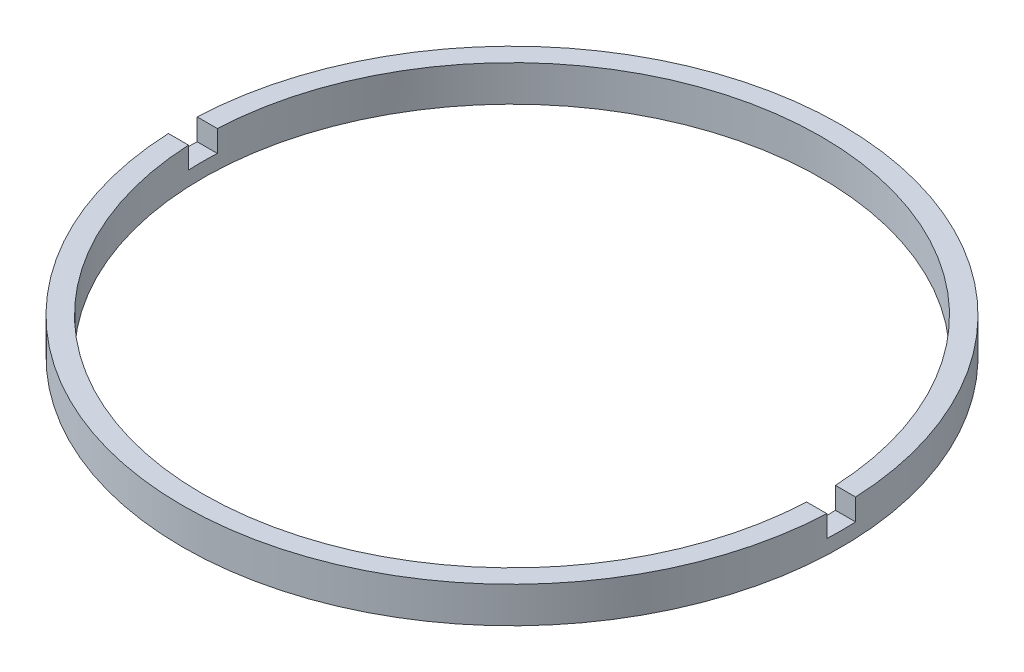
SolidWorks part; units mm, degrees
ref_plane "前视基准面" through (0, 0, 0) normal (0, 0, 1) x (1, 0, 0)
ref_plane "上视基准面" through (0, 0, 0) normal (0, 1, 0) x (1, 0, 0)
ref_plane "右视基准面" through (0, 0, 0) normal (1, 0, 0) x (0, 0, -1)
sketch "草图1" plane through (0, 0, 0) normal (0, 0, 1) x (1, 0, 0)
  line L0 (0, 56.2608) -> (0, -99.1922) construction
  line L1 (21.5, -1.9642) -> (22.9, -1.9642)
  line L4 (22.9, -1.9642) -> (22.9, -4.4642)
  line L5 (21.5, -4.4642) -> (21.5, -1.9642)
  line L7 (21.5, -4.4642) -> (22.9, -4.4642)
  dimension "D1" = 2.5
  dimension "D2" = 22.9
  dimension "D3" = 21.5
revolve "旋转1" add sketch "草图1" angle 360 about L0
cosmetic thread "装饰螺纹线1" parameters "D2"=45.7
sketch "草图2" plane through (0, -1.9642, 0) normal (0, 1, 0) x (1, 0, 0)
  line L0 (-28.67, 0) -> (29.9422, 0) construction
  line L2 (-26.8525, 1) -> (26.8525, 1)
  line L3 (-26.8525, 1) -> (-26.8525, -1)
  line L4 (-26.8525, -1) -> (26.8525, -1)
  line L5 (26.8525, 1) -> (26.8525, -1)
  line L6 (-26.8525, 1) -> (26.8525, -1) construction
  line L7 (-26.8525, -1) -> (26.8525, 1) construction
  point P3 (0, 0)
  dimension "D1" = 2
extrude "切除-拉伸1" cut sketch "草图2" against normal blind 1.5
